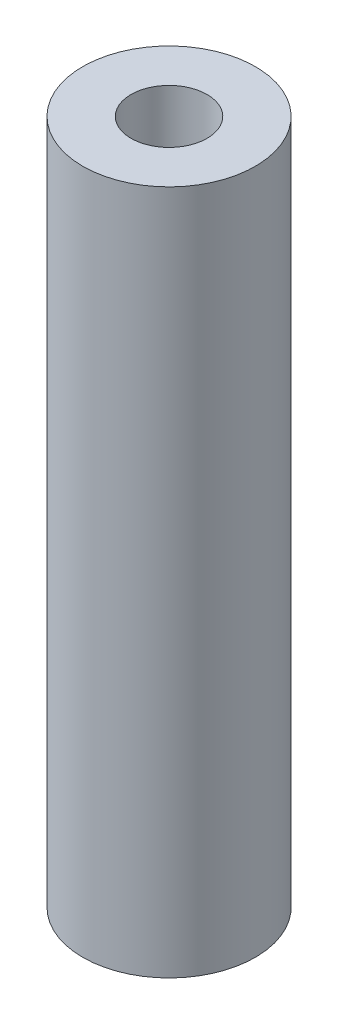
SolidWorks part; units mm, degrees
ref_plane "Front Plane" through (0, 0, 0) normal (0, 0, 1) x (1, 0, 0)
ref_plane "Top Plane" through (0, 0, 0) normal (0, 1, 0) x (1, 0, 0)
ref_plane "Right Plane" through (0, 0, 0) normal (1, 0, 0) x (0, 0, -1)
sketch "Sketch1" plane through (0, 0, 0) normal (0, 1, 0) x (1, 0, 0)
  circle A1 centre (0, 0) radius 3.2004
extrude "Boss-Extrude1" add sketch "Sketch1" along normal blind 25.4
hole_wizard "#34 (0.111) Diameter Hole1" positions "Sketch3" profile "Sketch4" hole size "#34" standard "ANSI Inch" end condition through all
sketch "Sketch3" plane through (0, 0, 0) normal (0, -1, 0) x (-1, 0, 0)
  point P0 (0, 0)
sketch "Sketch4" plane through (0, 0, 0) normal (1, 0, 0) x (0, 0, -1)
  line L0 (0, 0) -> (0, 25.4)
  line L1 (0, 25.4) -> (1.4097, 25.4)
  line L2 (1.4097, 25.4) -> (1.4097, 0)
  line L5 (1.4097, 0) -> (0, 0)
  line L11 (0, -6.35) -> (0, 107.95) construction
  dimension "Thru Hole Dia." = 2.8194
  dimension "Thru Hole Depth" = 25.4
